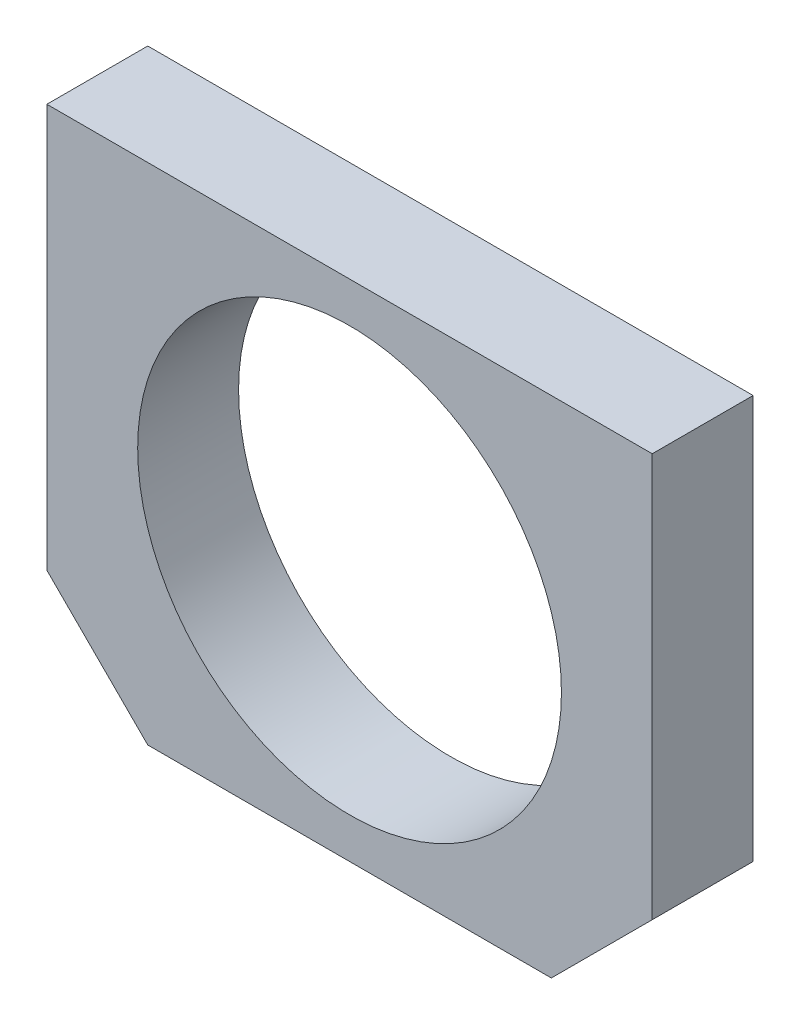
SolidWorks part; units mm, degrees
material "1060-H12"
ref_plane "Alzado" through (0, 0, 0) normal (0, 0, 1) x (1, 0, 0)
ref_plane "Planta" through (0, 0, 0) normal (0, 1, 0) x (1, 0, 0)
ref_plane "Vista lateral" through (0, 0, 0) normal (1, 0, 0) x (0, 0, -1)
sketch "Croquis1" plane through (0, 0, 0) normal (0, 0, 1) x (1, 0, 0)
  line L0 (-30, 25) -> (-30, -15)
  line L1 (-30, -15) -> (-20, -25)
  line L2 (-20, -25) -> (20, -25)
  line L3 (20, -25) -> (30, -15)
  line L4 (30, -15) -> (30, 25)
  line L5 (30, 25) -> (-30, 25)
  circle A0 centre (0, 0) radius 21
  dimension "D1" = 42
  dimension "D4" = 25
  dimension "D2" = 40
  dimension "D3" = 40
  dimension "D5" = 135
  dimension "D6" = 135
  dimension "D7" = 30
  dimension "D8" = 60
  dimension "D9" = 40
extrude "Saliente-Extruir1" add sketch "Croquis1" along normal blind 10
